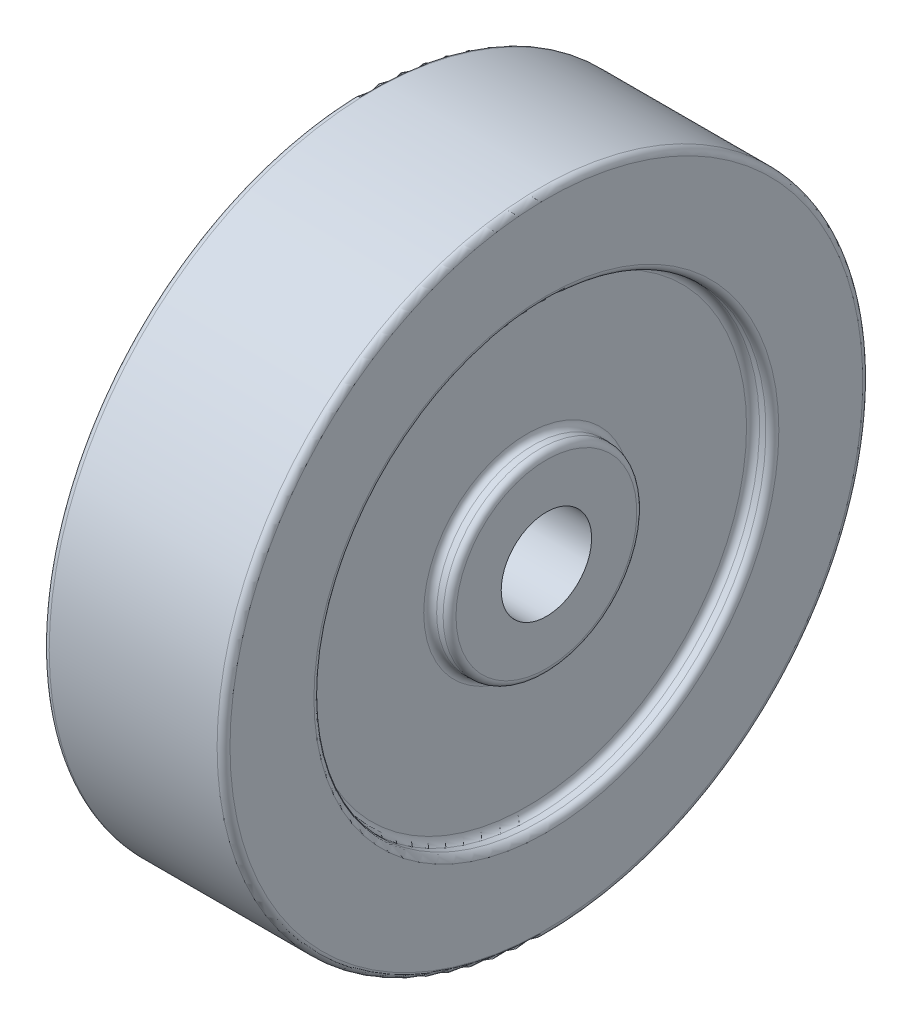
SolidWorks part; units mm, degrees
ref_plane "Front Plane" through (0, 0, 0) normal (0, 0, 1) x (1, 0, 0)
ref_plane "Top Plane" through (0, 0, 0) normal (0, 1, 0) x (1, 0, 0)
ref_plane "Right Plane" through (0, 0, 0) normal (1, 0, 0) x (0, 0, -1)
sketch "Sketch1" plane through (0, 0, 0) normal (0, 0, 1) x (1, 0, 0)
  line L0 (-90.0723, 0) -> (99.3494, 0) construction
  line L1 (0, 60.6386) -> (0, -63.3373) construction
  line L2 (14, 7) -> (14, 15)
  line L3 (14, 15) -> (11, 15)
  line L4 (11, 15) -> (11, 35)
  line L5 (11, 35) -> (14, 35)
  line L6 (14, 35) -> (14, 50)
  line L7 (-14, 35) -> (-14, 50)
  line L8 (-11, 35) -> (-14, 35)
  line L9 (-11, 15) -> (-11, 35)
  line L10 (-14, 15) -> (-11, 15)
  line L11 (-14, 7) -> (-14, 15)
  line L12 (-14, 50) -> (14, 50)
  line L13 (-14, 7) -> (14, 7)
  dimension "D1" = 14
  dimension "D2" = 30
  dimension "D3" = 70
  dimension "D4" = 100
  dimension "D5" = 28
  dimension "D6" = 3
revolve "Revolve1" add sketch "Sketch1" angle 360 about L0
fillet "Fillet1" radius 1 10 edges at (-14, 0, 15) (-11, 0, 35) (-11, 0, 15) (-14, 0, 35) (14, 0, 15) (11, 0, 15) (11, 0, 35) (14, 0, 35) (14, 0, 50) (-14, 0, 50)
